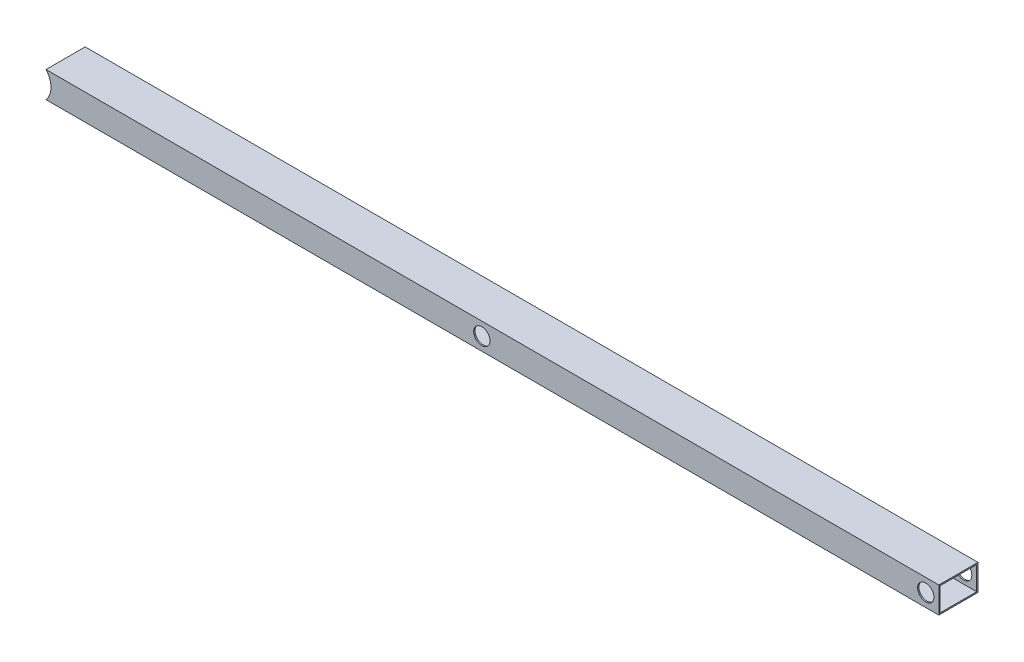
SolidWorks part; units mm, degrees
ref_plane "Front Plane" through (0, 0, 0) normal (0, 0, 1) x (1, 0, 0)
ref_plane "Top Plane" through (0, 0, 0) normal (0, 1, 0) x (1, 0, 0)
ref_plane "Right Plane" through (0, 0, 0) normal (1, 0, 0) x (0, 0, -1)
sketch "Sketch1" plane through (0, 0, 0) normal (0, 0, 1) x (1, 0, 0)
  line L1 (700, 20) -> (-700, 20)
  line L2 (700, 20) -> (700, -20)
  line L3 (700, -20) -> (-700, -20)
  line L4 (-700, 20) -> (-700, -20)
  line L5 (700, 20) -> (-700, -20) construction
  line L6 (700, -20) -> (-700, 20) construction
  circle A0 centre (0, 0) radius 12.5
  circle A1 centre (-690, 0) radius 30
  circle A2 centre (680, 0) radius 12.5
  point P0 (0, 0)
  dimension "D2" = 25
  dimension "D3" = 60
  dimension "D5" = 25
  dimension "D1" = 40
  dimension "D4" = 690
  dimension "D6" = 680
  dimension "D7" = 700
extrude "Boss-Extrude1" add sketch "Sketch1" along normal mid plane 60 contours A1 L3 L2 L1 A2 A0
sketch "Sketch2" plane through (700, 0, 0) normal (1, 0, 0) x (0, 0, -1)
  line L14 (28, -18) -> (28, 18)
  line L15 (-28, -18) -> (28, -18)
  line L16 (-28, 18) -> (-28, -18)
  line L17 (28, 18) -> (-28, 18)
  line L18 (28, -18) -> (28, 18)
  line L19 (-28, -18) -> (28, -18)
  line L20 (-28, 18) -> (-28, -18)
  line L21 (28, 18) -> (-28, 18)
  dimension "D1" = 2
extrude "Cut-Extrude1" cut sketch "Sketch2" against normal through all
